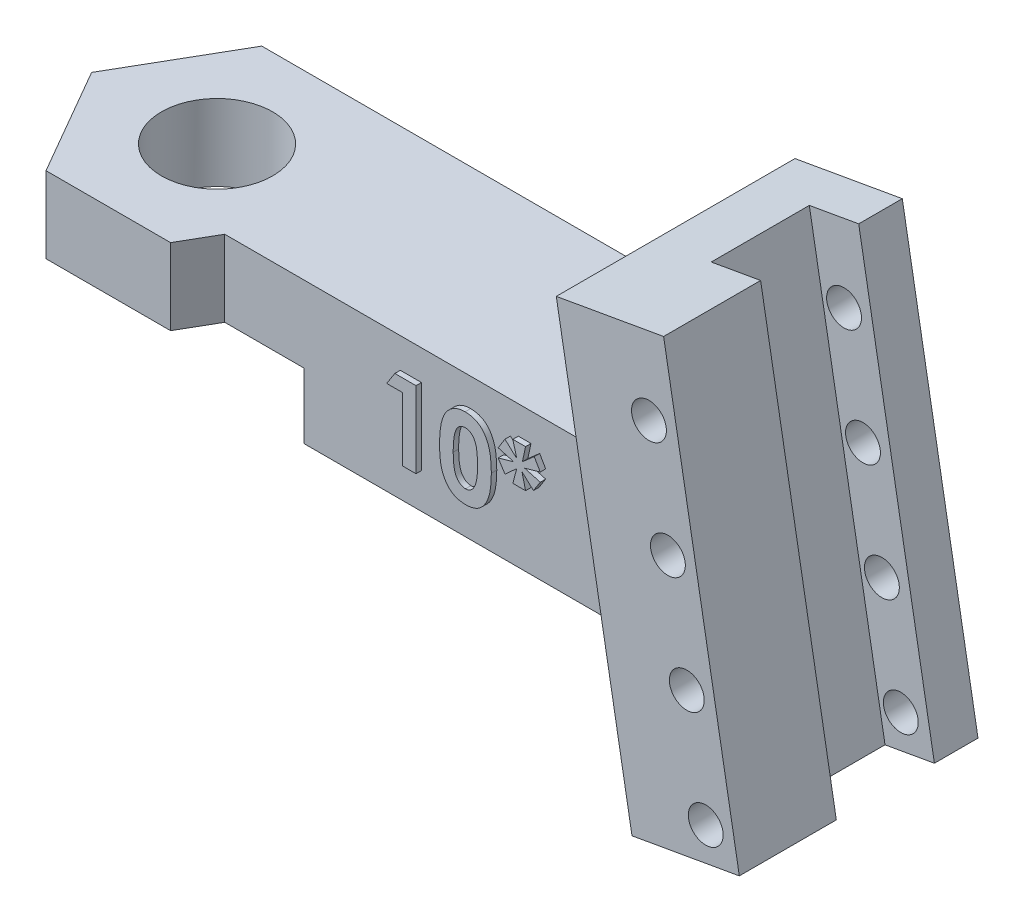
SolidWorks part; units mm, degrees
ref_plane "Front Plane" through (0, 0, 0) normal (0, 0, 1) x (1, 0, 0)
ref_plane "Top Plane" through (0, 0, 0) normal (0, 1, 0) x (1, 0, 0)
ref_plane "Right Plane" through (0, 0, 0) normal (1, 0, 0) x (0, 0, -1)
sketch "Sketch1" plane through (0, 0, 0) normal (0, 1, 0) x (1, 0, 0)
  line L1 (0, 0) -> (25, 0)
  line L2 (0, 0) -> (0, -6.75)
  line L3 (0, -6.75) -> (25, -6.75)
  line L4 (25, 0) -> (25, -6.75)
  dimension "D1" = 6.75
  dimension "D2" = 25
extrude "Boss-Extrude1" add sketch "Sketch1" along normal blind 6.5
ref_plane "Plane1" through (0, 0, 3.375) normal (0, 0, 1) x (1, 0, 0)
sketch "Sketch5" plane through (0, 6.5, 0) normal (0, 1, 0) x (1, 0, 0)
  line L0 (0, 0) -> (0, -6.75) construction
  line L1 (-5.7158, -3.375) -> (-2.8579, -8.325)
  line L2 (-2.8579, -8.325) -> (2.8579, -8.325)
  line L3 (2.8579, -8.325) -> (5.7158, -3.375)
  line L4 (5.7158, -3.375) -> (2.8579, 1.575)
  line L5 (2.8579, 1.575) -> (-2.8579, 1.575)
  line L6 (-2.8579, 1.575) -> (-5.7158, -3.375)
  circle A0 centre (0, -3.375) radius 4.95 construction
  dimension "D1" = 4.95
extrude "Boss-Extrude4" add sketch "Sketch5" against normal up to surface (6.5 mm away) up to face at (12.5, 0, 3.375)
sketch "Sketch3" plane through (0, 0, 3.375) normal (0, 0, 1) x (1, 0, 0)
  line L0 (21.603, 14.262) -> (26.527, 15.1303)
  line L1 (26.527, 15.1303) -> (30, -4.5659)
  line L2 (30, -4.5659) -> (25.076, -5.4341)
  line L3 (25.076, -5.4341) -> (21.603, 14.262)
  line L4 (3.7672, 6.5) -> (25, 6.5) construction
  point P6 (27.538, -5)
  dimension "D1" = 30
  dimension "D2" = 5
  dimension "D3" = 20
  dimension "D4" = 80
  dimension "D6" = 5
extrude "Boss-Extrude3" add sketch "Sketch3" against normal up to surface (4.95 mm away) and the other way blind 6 up to face at (0, 3.25, -1.575)
sketch "Sketch4" plane through (-1.7875, 10.1377, 0) normal (-0.1736, 0.9848, 0) x (0.9848, 0.1736, 0)
  line L0 (28.7514, -9.375) -> (28.7514, 1.575) construction
  line L1 (26.4514, -0.425) -> (28.7514, -0.425)
  line L2 (26.4514, -0.425) -> (26.4514, -4.925)
  line L3 (26.4514, -4.925) -> (28.7514, -4.925)
  line L4 (28.7514, -0.425) -> (28.7514, -4.925)
  line L6 (28.7514, 1.575) -> (23.7514, 1.575) construction
  dimension "D1" = 4.5
  dimension "D2" = 2.3
  dimension "D3" = 2
extrude "Cut-Extrude1" cut sketch "Sketch4" against normal blind 23 contours L2 L3 L4 L1
sketch "Sketch6" plane through (0, 6.5, 0) normal (0, 1, 0) x (1, 0, 0)
  circle A0 centre (0, -3.3356) radius 2.55
  dimension "D1" = 5.1
extrude "Cut-Extrude2" cut sketch "Sketch6" against normal blind 10
sketch "Sketch7" plane through (0, 0, -1.575) normal (0, 0, -1) x (-1, 0, 0)
  line L0 (-2.8579, 0) -> (-24.1178, 0)
  line L1 (-24.1178, 0) -> (-25.076, -5.4341)
  line L2 (-25.076, -5.4341) -> (-30, -4.5659)
  line L3 (-30, -4.5659) -> (-26.527, 15.1303)
  line L4 (-26.527, 15.1303) -> (-21.603, 14.262)
  line L5 (-21.603, 14.262) -> (-22.9717, 6.5)
  line L6 (-22.9717, 6.5) -> (-2.8579, 6.5)
  line L7 (-2.8579, 6.5) -> (-2.8579, 0)
  dimension "D1" = 20
extrude "Boss-Extrude5" add sketch "Sketch7" against normal up to surface (1.575 mm away) up to face at (13.656, 3.25, 0)
sketch "Sketch8" plane through (0, 0, 0) normal (0, -1, 0) x (-1, 0, 0)
  line L1 (-4.6765, -11.475) -> (4.6765, -11.475)
  line L2 (4.6765, -11.475) -> (9.3531, -3.375)
  line L3 (9.3531, -3.375) -> (4.6765, 4.725)
  line L4 (4.6765, 4.725) -> (-4.6765, 4.725)
  line L5 (-4.6765, 4.725) -> (-9.3531, -3.375)
  line L6 (-9.3531, -3.375) -> (-4.6765, -11.475)
  circle A0 centre (0, -3.375) radius 8.1 construction
  dimension "D1" = 16.2
extrude "Cut-Extrude3" cut sketch "Sketch8" against normal blind 3
sketch "Sketch9" plane through (0, 0, -1.575) normal (0, 0, -1) x (-1, 0, 0)
  line L0 (-30, -4.5659) -> (-26.527, 15.1303) construction
  line L1 (-25.076, -5.4341) -> (-30, -4.5659) construction
  line L2 (-28.4593, -3.3144) -> (-25.8546, 11.4577) construction
  line L3 (-30, -4.5659) -> (-26.527, 15.1303) construction
  circle A0 centre (-28.4593, -3.3144) radius 0.8
  circle A4 centre (-27.591, 1.6096) radius 0.8
  circle A5 centre (-26.7228, 6.5337) radius 0.8
  circle A6 centre (-25.8546, 11.4577) radius 0.8
  dimension "D1" = 1.6
  dimension "D2" = 1.3
  dimension "D5" = 5
  dimension "D3" = 1.5
  dimension "D4" = 5
  dimension "D6" = 5
extrude "Cut-Extrude4" cut sketch "Sketch9" against normal up to surface (10.95 mm away) up to face at (25.8015, 4.8481, 9.375)
sketch "Sketch10" plane through (0, 0, 6.75) normal (0, 0, 1) x (1, 0, 0)
  text T0 "<b>10*</b>"
extrude "Boss-Extrude6" add sketch "Sketch10" along normal blind 0.25
